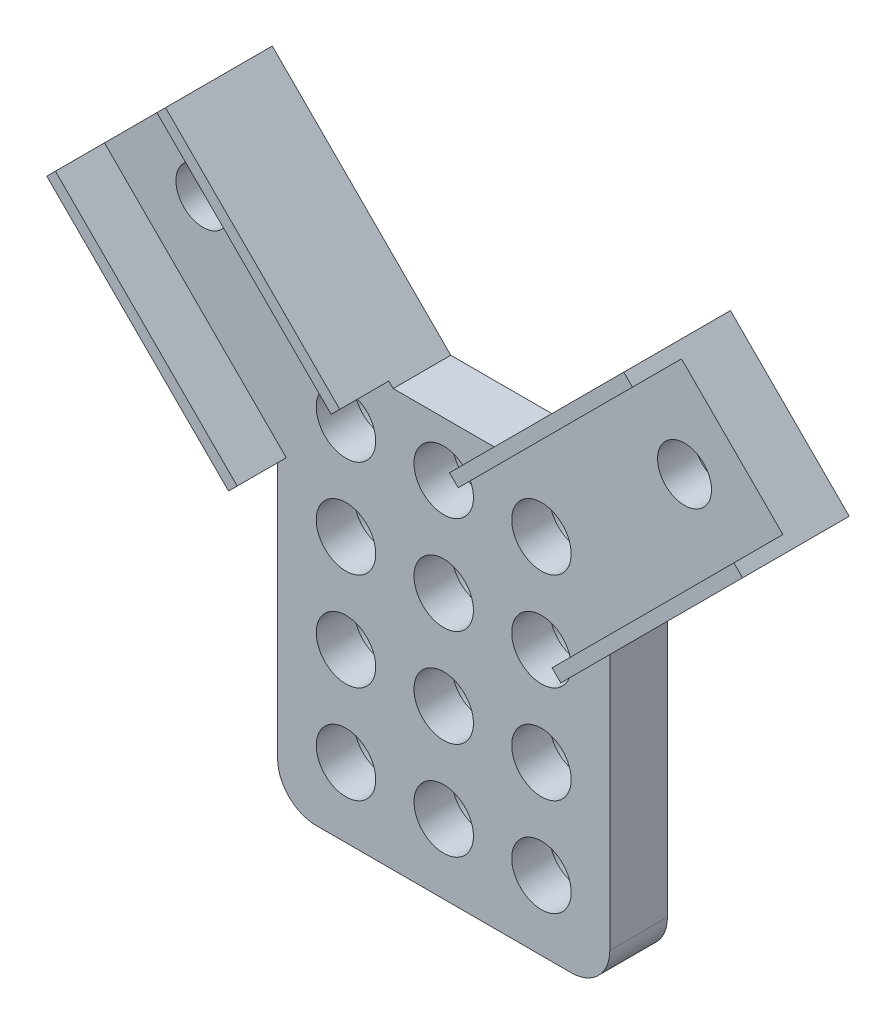
SolidWorks part; units mm, degrees
ref_plane "Přední rovina" through (0, 0, 0) normal (0, 0, 1) x (1, 0, 0)
ref_plane "Horní rovina" through (0, 0, 0) normal (0, 1, 0) x (1, 0, 0)
ref_plane "Pravá rovina" through (0, 0, 0) normal (1, 0, 0) x (0, 0, -1)
sketch "Skica1" plane through (0, 0, 0) normal (0, 0, 1) x (1, 0, 0)
  line L1 (3.15, 0) -> (23.94, 0)
  line L2 (0, 3.15) -> (0, 34)
  line L3 (0, 34) -> (27.09, 34)
  line L4 (27.09, 3.15) -> (27.09, 34)
  arc A0 (3.15, 0) -> (0, 3.15) centre (3.15, 3.15) cw
  arc A1 (23.94, 0) -> (27.09, 3.15) centre (23.94, 3.15) ccw
  point P7 (0, 0)
  point P10 (27.09, 0)
  dimension "D3" = 3.15
  dimension "D4" = 3.15
  dimension "D1" = 27.09
  dimension "D2" = 34
extrude "Přidat vysunutím1" add sketch "Skica1" along normal blind 4.7
sketch "Skica2" plane through (0, 0, 0) normal (0, 0, -1) x (-1, 0, 0)
  line L4 (-9.7116, 33.7116) -> (-0.0242, 24.0242)
  line L5 (-27.09, 3.15) -> (-27.09, 34) construction
  line L6 (-27.09, 34) -> (0, 34) construction
  line L7 (-9.7116, 33.7116) -> (5.1377, 48.5608)
  line L8 (-0.0242, 24.0242) -> (14.825, 38.8735)
  line L9 (-41.915, 38.8735) -> (-27.0658, 24.0242)
  line L10 (-41.915, 38.8735) -> (-32.2277, 48.5608)
  line L11 (-27.0658, 24.0242) -> (-17.3784, 33.7116)
  line L12 (-32.2277, 48.5608) -> (-17.3784, 33.7116)
  line L13 (5.1377, 48.5608) -> (14.825, 38.8735)
  line L14 (0, 34) -> (0, 3.15) construction
  circle A0 centre (-21.515, 29.575) radius 2.425 construction
  circle A1 centre (-5.575, 29.575) radius 2.425 construction
  dimension "D1" = 4.85
  dimension "D2" = 15.94
  dimension "D3" = 5.85
  dimension "D4" = 3.15
  dimension "D5" = 2
  dimension "D6" = 7.85
  dimension "D7" = 21
  dimension "D8" = 0
  dimension "D9" = 45
  dimension "D10" = 21
  dimension "D11" = 5.85
  dimension "D12" = 7.85
  dimension "D13" = 0
  dimension "D14" = 45
extrude "Přidat vysunutím2" add sketch "Skica2" against normal blind 4.7
sketch "Skica3" plane through (0, 0, 4.7) normal (0, 0, 1) x (1, 0, 0)
  line L0 (0, 24.0484) -> (0, 3.15) construction
  line L2 (17.6669, 34) -> (9.4231, 34) construction
  circle A0 centre (5.575, 29.575) radius 2.425
  circle A1 centre (13.545, 29.575) radius 2.425
  circle A2 centre (21.515, 29.575) radius 2.425
  circle A3 centre (5.575, 21.605) radius 2.425
  circle A4 centre (13.545, 21.605) radius 2.425
  circle A5 centre (21.515, 21.605) radius 2.425
  circle A6 centre (21.515, 13.635) radius 2.425
  circle A7 centre (13.545, 13.635) radius 2.425
  circle A8 centre (5.575, 13.635) radius 2.425
  circle A9 centre (5.575, 5.665) radius 2.425
  circle A10 centre (13.545, 5.665) radius 2.425
  circle A11 centre (21.515, 5.665) radius 2.425
  dimension "D1" = 4.85
  dimension "D2" = 7.97
  dimension "D3" = 7.97
  dimension "D4" = 3.15
  dimension "D5" = 7.97
  dimension "D6" = 7.97
  dimension "D7" = 7.97
  dimension "D8" = 2
extrude "Odebrat vysunutím1" cut sketch "Skica3" against normal blind 14.6
sketch "Skica4" plane through (0, 0, 4.7) normal (0, 0, 1) x (1, 0, 0)
  line L0 (-5.1377, 48.5608) -> (9.0696, 34.3536)
  line L1 (-5.1377, 48.5608) -> (-5.8448, 47.8537)
  line L2 (9.0696, 34.3536) -> (8.3625, 33.6464)
  line L3 (-5.8448, 47.8537) -> (8.3625, 33.6464)
  line L4 (-5.1377, 48.5608) -> (9.4231, 34) construction
  line L5 (32.2277, 48.5608) -> (18.0204, 34.3536)
  line L6 (32.2277, 48.5608) -> (32.9348, 47.8537)
  line L7 (18.0204, 34.3536) -> (18.7275, 33.6464)
  line L8 (32.9348, 47.8537) -> (18.7275, 33.6464)
  line L9 (17.6669, 34) -> (32.2277, 48.5608) construction
  line L10 (-14.825, 38.8735) -> (0, 24.0484)
  line L11 (-14.825, 38.8735) -> (-14.1179, 39.5806)
  line L12 (0, 24.0484) -> (0.7071, 24.7555)
  line L13 (-14.1179, 39.5806) -> (0.7071, 24.7555)
  line L14 (41.915, 38.8735) -> (27.09, 24.0484)
  line L15 (41.915, 38.8735) -> (41.2079, 39.5806)
  line L16 (27.09, 24.0484) -> (26.3829, 24.7555)
  line L17 (41.2079, 39.5806) -> (26.3829, 24.7555)
  dimension "D1" = 0.5
  dimension "D2" = 1
  dimension "D3" = 1
  dimension "D4" = 0.5
  dimension "D5" = 1
  dimension "D6" = 1
extrude "Přidat vysunutím3" add sketch "Skica4" along normal blind 4
sketch "Skica5" plane through (0, 0, 0) normal (0, 0, -1) x (-1, 0, 0)
  circle A0 centre (-21.515, 29.575) radius 3
  circle A1 centre (-13.545, 29.575) radius 3
  circle A2 centre (-5.575, 29.575) radius 3
  circle A3 centre (-5.575, 21.605) radius 3
  circle A4 centre (-13.545, 21.605) radius 3
  circle A5 centre (-21.515, 21.605) radius 3
  circle A6 centre (-13.545, 5.665) radius 3
  circle A7 centre (-21.515, 5.665) radius 3
  circle A8 centre (-5.575, 5.665) radius 3
  circle A9 centre (-5.575, 13.635) radius 3
  circle A10 centre (-13.545, 13.635) radius 3
  circle A11 centre (-21.515, 13.635) radius 3
  dimension "D1" = 6
extrude "Odebrat vysunutím2" cut sketch "Skica5" against normal blind 1.6
sketch "Sketch1" plane through (0, 0, 4.7) normal (0, 0, 1) x (1, 0, 0)
  line L1 (9.0696, 34.3536) -> (-5.1377, 48.5608) construction
  line L3 (-14.1179, 39.5806) -> (-5.8448, 47.8537) construction
  line L4 (27.09, 24.0484) -> (41.915, 38.8735) construction
  line L5 (32.9348, 47.8537) -> (41.2079, 39.5806) construction
  circle A0 centre (-6.0923, 39.828) radius 2.2
  circle A1 centre (33.1823, 39.828) radius 2.2
  dimension "D1" = 4.4
  dimension "D2" = 6.85
  dimension "D3" = 5.5
  dimension "D4" = 6.85
  dimension "D5" = 5.5
extrude "Cut-Extrude1" cut sketch "Sketch1" against normal blind 3
